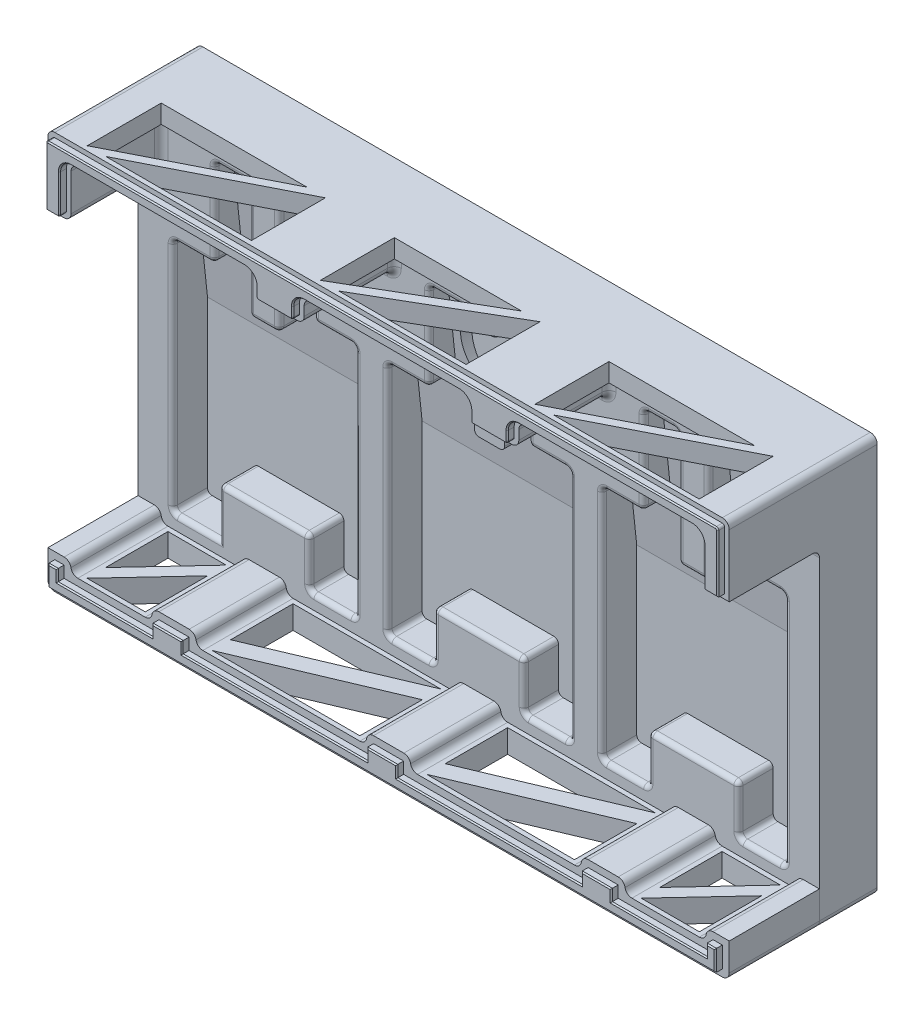
SolidWorks part; units mm, degrees
material "PP generico"
ref_plane "Piano frontale" through (0, 0, 0) normal (0, 0, 1) x (1, 0, 0)
ref_plane "Piano superiore" through (0, 0, 0) normal (0, 1, 0) x (1, 0, 0)
ref_plane "Piano destro" through (0, 0, 0) normal (1, 0, 0) x (0, 0, -1)
sketch "Schizzo1" plane through (0, 0, 0) normal (0, 0, 1) x (1, 0, 0)
  line L1 (-147.3, 86) -> (147.3, 86)
  line L2 (-147.3, 86) -> (-147.3, -86)
  line L3 (-147.3, -86) -> (147.3, -86)
  line L4 (147.3, 86) -> (147.3, -86)
  dimension "D1" = 294.6
  dimension "D2" = 172
  dimension "D3" = 147.3
  dimension "D4" = 86
extrude "Estrusione-Estrusione1" add sketch "Schizzo1" along normal blind 10 contours L1 L4 L3 L2
sketch "Schizzo2" plane through (0, 0, 10) normal (0, 0, 1) x (1, 0, 0)
  line L0 (-73.3, -70) -> (-53.3, -70)
  line L1 (-147.3, 86) -> (147.3, 86)
  line L2 (-147.3, 86) -> (-147.3, -86)
  line L3 (-6.3232, -86) -> (147.3, -86)
  line L4 (147.3, 86) -> (147.3, -86)
  line L9 (-114.3, 70) -> (-99.3, 70)
  line L10 (-132.3, 32) -> (-132.3, -70)
  line L11 (-132.3, -70) -> (-112.3, -70)
  line L12 (-53.3, 32) -> (-53.3, -70)
  line L14 (-39.5, 32) -> (-39.5, -69.8088)
  line L15 (-39.5, -69.8088) -> (-19.5, -69.8088)
  line L16 (39.5, 32) -> (39.5, -69.8088)
  line L18 (53.3, 32) -> (53.3, -69.8088)
  line L19 (53.3, -69.8088) -> (73.3, -69.8088)
  line L20 (132.3, 32) -> (132.3, -69.8088)
  line L21 (-112.3, -49) -> (-73.3, -49)
  line L22 (-112.3, -49) -> (-112.3, -70)
  line L24 (-73.3, -49) -> (-73.3, -70)
  line L25 (19.5, -69.8088) -> (39.5, -69.8088)
  line L26 (-19.5, -48.8088) -> (19.5, -48.8088)
  line L27 (-19.5, -48.8088) -> (-19.5, -69.8088)
  line L29 (19.5, -48.8088) -> (19.5, -69.8088)
  line L30 (73.3, -48.8088) -> (112.3, -48.8088)
  line L31 (73.3, -48.8088) -> (73.3, -69.8088)
  line L33 (112.3, -48.8088) -> (112.3, -69.8088)
  line L34 (112.3, -69.8088) -> (132.3, -69.8088)
  line L35 (-86.3, 70) -> (-71.3, 70)
  line L38 (-132.3, 32) -> (-114.3, 32)
  line L39 (-114.3, 70) -> (-114.3, 32)
  line L42 (-53.3, 32) -> (-71.3, 32)
  line L43 (-71.3, 70) -> (-71.3, 32)
  line L45 (-99.3, 70) -> (-99.3, 20)
  line L46 (-99.3, 20) -> (-86.3, 20)
  line L47 (-86.3, 70) -> (-86.3, 20)
  line L48 (-21.5, 70) -> (-21.5, 32)
  line L49 (-39.5, 32) -> (-21.5, 32)
  line L50 (-21.5, 70) -> (-6.5, 70)
  line L51 (-6.5, 70) -> (-6.5, 20)
  line L52 (6.5, 70) -> (6.5, 20)
  line L53 (6.5, 70) -> (21.5, 70)
  line L54 (21.5, 70) -> (21.5, 32)
  line L55 (39.5, 32) -> (21.5, 32)
  line L56 (-6.5, 20) -> (6.5, 20)
  line L57 (71.3, 70) -> (71.3, 32)
  line L58 (53.3, 32) -> (71.3, 32)
  line L59 (71.3, 70) -> (86.3, 70)
  line L60 (86.3, 70) -> (86.3, 20)
  line L61 (99.3, 70) -> (99.3, 20)
  line L62 (99.3, 70) -> (114.3, 70)
  line L63 (114.3, 70) -> (114.3, 32)
  line L64 (132.3, 32) -> (114.3, 32)
  line L65 (86.3, 20) -> (99.3, 20)
  dimension "D3" = 15
  dimension "D4" = 13.8
  dimension "D5" = 140
  dimension "D6" = 38
  dimension "D7" = 38
  dimension "D8" = 20
  dimension "D9" = 20
  dimension "D10" = 21
  dimension "D11" = 20
  dimension "D12" = 20
  dimension "D13" = 16
  dimension "D14" = 0
  dimension "D16" = 20
  dimension "D17" = 20
  dimension "D18" = 21
  dimension "D19" = 21
  dimension "D20" = 18
  dimension "D21" = 18
  dimension "D22" = 15
  dimension "D23" = 15
  dimension "D24" = 50
  dimension "D25" = 3
extrude "Estrusione-Estrusione2" add sketch "Schizzo2" along normal blind 15
sketch "Schizzo4" plane through (132.3, 0, 0) normal (-1, 0, 0) x (0, 0, 1)
  line L0 (10, 70) -> (10, 3.34)
  line L1 (10, 32) -> (10, -69.8088) construction
  line L2 (10, 3.34) -> (17.12, 70)
  line L4 (17.12, 70) -> (10, 70)
  dimension "D3" = 73.1488
extrude "Estrusione-Estrusione3" add sketch "Schizzo4" along normal up to surface (264.6 mm away) up to face at (-132.3, -19, 17.5)
sketch "Schizzo5" plane through (0, 0, 25) normal (0, 0, 1) x (1, 0, 0)
  line L0 (-147.3, 86) -> (-147.3, 56)
  line L1 (-147.3, 86) -> (-147.3, -86) construction
  line L2 (-147.3, 56) -> (-137.3, 56)
  line L3 (-137.3, 56) -> (-137.3, 78)
  line L4 (-137.3, 78) -> (-56.3, 78)
  line L5 (-56.3, 78) -> (-56.3, 68)
  line L6 (-56.3, 68) -> (-36.5, 68)
  line L7 (-36.5, 68) -> (-36.5, 78)
  line L8 (-36.5, 78) -> (36.5, 78)
  line L9 (36.5, 78) -> (36.5, 68)
  line L10 (36.5, 68) -> (56.3, 68)
  line L11 (56.3, 68) -> (56.3, 78)
  line L12 (56.3, 78) -> (137.3, 78)
  line L13 (137.3, 78) -> (137.3, 56)
  line L14 (137.3, 56) -> (147.3, 56)
  line L15 (147.3, -86) -> (147.3, 86) construction
  line L16 (147.3, 56) -> (147.3, 86)
  line L17 (147.3, 86) -> (-147.3, 86)
  line L18 (-21.5, 70) -> (-21.5, 32) construction
  line L19 (-71.3, 32) -> (-71.3, 70) construction
  line L20 (21.5, 32) -> (21.5, 70) construction
  line L22 (71.3, 70) -> (71.3, 32) construction
  dimension "D1" = 30
  dimension "D2" = 30
  dimension "D3" = 10
  dimension "D4" = 10
  dimension "D5" = 15
  dimension "D6" = 15
  dimension "D7" = 8
  dimension "D8" = 15
  dimension "D9" = 8
  dimension "D10" = 15
  dimension "D11" = 8
extrude "Estrusione-Estrusione4" add sketch "Schizzo5" along normal blind 39
fillet "Raccordo1" radius 3 27 edges at (137.3, 67, 25) (36.5, 73, 25) (56.3, 73, 25) (-36.5, 73, 25) (-56.3, 73, 25) (147.3, 86, 32) (137.3, 78, 44.5) (137.3, 56, 44.5) (142.3, 56, 25) (96.8, 78, 25) (56.3, 78, 44.5) (36.5, 78, 44.5) (36.5, 68, 44.5) (56.3, 68, 44.5) (46.4, 68, 25) (0, 78, 25) (-36.5, 68, 44.5) (-36.5, 78, 44.5) (-46.4, 68, 25) (-56.3, 68, 44.5) (-147.3, 86, 32) (-137.3, 56, 44.5) (-137.3, 78, 44.5) (-96.8, 78, 25) (-142.3, 56, 25) (-137.3, 67, 25) (-56.3, 78, 44.5)
fillet "Raccordo2" radius 2 31 edges at (-114.3, 51, 25) (-123.3, 32, 25) (-53.3, -70, 17.5) (-132.3, -70, 17.5) (-112.3, -49, 17.5) (-73.3, -70, 17.5) (-73.3, -49, 17.5) (-53.3, 32, 19.0306) (-99.3, 70, 21.06) (-86.3, 70, 21.06) (-71.3, 70, 21.06) (-71.3, 32, 19.0306) (-86.3, 20, 18.3897) (-99.3, 20, 18.3897) (-71.3, 51, 25) (-86.3, 45, 25) (-99.3, 45, 25) (-92.8, 20, 25) (-106.8, 70, 25) (-78.8, 70, 25) (-62.3, 32, 25) (-53.3, -19, 25) (-63.3, -70, 25) (-73.3, -59.5, 25) (-92.8, -49, 25) (-112.3, -59.5, 25) (-122.3, -70, 25) (-132.3, -19, 25) (-114.3, 70, 21.06) (-132.3, 32, 19.0306) (-114.3, 32, 19.0306)
fillet "Raccordo4" radius 2 64 edges at (114.3, 51, 25) (106.8, 70, 25) (78.8, 70, 25) (53.3, -18.9044, 25) (132.3, -69.8088, 17.5) (132.3, 32, 19.0306) (86.3, 20, 18.3897) (114.3, 32, 19.0306) (114.3, 70, 21.06) (99.3, 70, 21.06) (86.3, 70, 21.06) (71.3, 51, 25) (71.3, 70, 21.06) (53.3, 32, 19.0306) (73.3, -69.8088, 17.5) (73.3, -48.8088, 17.5) (112.3, -69.8088, 17.5) (132.3, -18.9044, 25) (123.3, 32, 25) (99.3, 45, 25) (86.3, 45, 25) (92.8, 20, 25) (62.3, 32, 25) (92.8, -48.8088, 25) (63.3, -69.8088, 25) (73.3, -59.3088, 25) (112.3, -59.3088, 25) (122.3, -69.8088, 25) (112.3, -48.8088, 17.5) (99.3, 20, 18.3897) (71.3, 32, 19.0306) (53.3, -69.8088, 17.5) (-39.5, -69.8088, 17.5) (19.5, -69.8088, 17.5) (39.5, -69.8088, 17.5) (19.5, -48.8088, 17.5) (-19.5, -48.8088, 17.5) (-19.5, -69.8088, 17.5) (-39.5, 32, 19.0306) (-21.5, 70, 21.06) (6.5, 70, 21.06) (21.5, 70, 21.06) (39.5, 32, 19.0306) (-21.5, 32, 19.0306) (-6.5, 20, 18.3897) (6.5, 20, 18.3897) (21.5, 32, 19.0306) (30.5, 32, 25) (21.5, 51, 25) (6.5, 45, 25) (-21.5, 51, 25) (-30.5, 32, 25) (-6.5, 45, 25) (0, 20, 25) (39.5, -18.9044, 25) (29.5, -69.8088, 25) (19.5, -59.3088, 25) (0, -48.8088, 25) (-19.5, -59.3088, 25) (-39.5, -18.9044, 25) (-29.5, -69.8088, 25) (-14, 70, 25) (14, 70, 25) (-6.5, 70, 21.06)
sketch "Schizzo8" plane through (0, 0, 25) normal (0, 0, 1) x (1, 0, 0)
  line L0 (-147.3, -86) -> (-147.3, -71)
  line L1 (-147.3, 53) -> (-147.3, -86) construction
  line L2 (-147.3, -71) -> (-137.3, -71)
  line L3 (-137.3, -71) -> (-137.3, -76)
  line L4 (-137.3, -76) -> (-102.3, -76)
  line L5 (-102.3, -76) -> (-102.3, -71)
  line L6 (-102.3, -71) -> (-83.3, -71)
  line L7 (-83.3, -71) -> (-83.3, -76)
  line L8 (-83.3, -76) -> (-9.5, -76)
  line L9 (-9.5, -76) -> (-9.5, -71)
  line L10 (-9.5, -71) -> (9.5, -71)
  line L11 (9.5, -71) -> (9.5, -76)
  line L12 (9.5, -76) -> (83.3, -76)
  line L13 (83.3, -76) -> (83.3, -71)
  line L14 (83.3, -71) -> (102.3, -71)
  line L15 (102.3, -71) -> (102.3, -76)
  line L16 (102.3, -76) -> (137.3, -76)
  line L17 (137.3, -76) -> (137.3, -71)
  line L18 (137.3, -71) -> (147.3, -71)
  line L19 (147.3, -86) -> (147.3, 53) construction
  line L20 (147.3, -71) -> (147.3, -86)
  line L21 (147.3, -86) -> (-147.3, -86)
  line L22 (-110.3, -51) -> (-110.3, -72) construction
  line L23 (-75.3, -68) -> (-75.3, -51) construction
  line L26 (75.3, -50.8088) -> (75.3, -67.8088) construction
  line L27 (110.3, -67.8088) -> (110.3, -50.8088) construction
  line L28 (-17.5, -50.8088) -> (-17.5, -67.8088) construction
  line L29 (17.5, -67.8088) -> (17.5, -50.8088) construction
  dimension "D1" = 10
  dimension "D2" = 10
  dimension "D3" = 15
  dimension "D4" = 15
  dimension "D5" = 15
  dimension "D6" = 15
  dimension "D7" = 15
  dimension "D8" = 8
  dimension "D9" = 8
  dimension "D10" = 8
  dimension "D11" = 8
  dimension "D12" = 8
  dimension "D13" = 8
  dimension "D14" = 10
  dimension "D15" = 10
  dimension "D16" = 10
  dimension "D17" = 10
extrude "Estrusione-Estrusione5" add sketch "Schizzo8" along normal up to surface (39 mm away) up to face at (0, 71.8414, 64)
fillet "Raccordo8" radius 3 2 edges at (147.3, -86, 12.5) (-147.3, -86, 12.5)
sketch "Schizzo10" plane through (0, 0, 64) normal (0, 0, 1) x (1, 0, 0)
  line L16 (-38.5, 71) -> (-38.5, 75)
  line L17 (-38.5, 71) -> (-38.5, 75)
  line L18 (140.3, -74) -> (140.3, -79)
  line L19 (140.3, -74) -> (140.3, -79)
  line L20 (99.3, -79) -> (99.3, -74)
  line L21 (99.3, -79) -> (99.3, -74)
  line L22 (86.3, -74) -> (86.3, -79)
  line L23 (86.3, -74) -> (86.3, -79)
  line L24 (6.5, -79) -> (6.5, -74)
  line L25 (6.5, -79) -> (6.5, -74)
  line L26 (-6.5, -74) -> (-6.5, -79)
  line L27 (-6.5, -74) -> (-6.5, -79)
  line L28 (-86.3, -79) -> (-86.3, -74)
  line L29 (-86.3, -79) -> (-86.3, -74)
  line L30 (38.5, 75) -> (38.5, 71)
  line L31 (38.5, 75) -> (38.5, 71)
  line L32 (-99.3, -74) -> (-99.3, -79)
  line L33 (-99.3, -74) -> (-99.3, -79)
  line L34 (-140.3, -79) -> (-140.3, -74)
  line L35 (-140.3, -79) -> (-140.3, -74)
  line L72 (-144.3, -83) -> (144.3, -83)
  line L73 (144.3, -83) -> (144.3, -74)
  line L74 (144.3, -74) -> (140.3, -74)
  line L75 (140.3, -79) -> (99.3, -79)
  line L76 (99.3, -74) -> (86.3, -74)
  line L77 (86.3, -79) -> (6.5, -79)
  line L78 (6.5, -74) -> (-6.5, -74)
  line L79 (-6.5, -79) -> (-86.3, -79)
  line L80 (-86.3, -74) -> (-99.3, -74)
  line L81 (-99.3, -79) -> (-140.3, -79)
  line L82 (-140.3, -74) -> (-144.3, -74)
  line L83 (-144.3, -74) -> (-144.3, -83)
  line L84 (-144.3, -83) -> (144.3, -83)
  line L85 (144.3, -83) -> (144.3, -74)
  line L86 (144.3, -74) -> (140.3, -74)
  line L87 (140.3, -79) -> (99.3, -79)
  line L88 (99.3, -74) -> (86.3, -74)
  line L89 (86.3, -79) -> (6.5, -79)
  line L90 (6.5, -74) -> (-6.5, -74)
  line L91 (-6.5, -79) -> (-86.3, -79)
  line L92 (-86.3, -74) -> (-99.3, -74)
  line L93 (-99.3, -79) -> (-140.3, -79)
  line L94 (-140.3, -74) -> (-144.3, -74)
  line L95 (-144.3, -74) -> (-144.3, -83)
  line L100 (140.3, 58) -> (145.3, 58)
  line L101 (145.3, 58) -> (145.3, 83)
  line L102 (144.3, 84) -> (-144.3, 84)
  line L103 (-145.3, 83) -> (-145.3, 58)
  line L104 (-145.3, 58) -> (-140.3, 58)
  line L105 (-139.3, 59) -> (-139.3, 75)
  line L106 (-134.3, 80) -> (-59.3, 80)
  line L107 (-54.3, 75) -> (-54.3, 71)
  line L108 (-53.3, 70) -> (-39.5, 70)
  line L110 (-33.5, 80) -> (33.5, 80)
  line L112 (39.5, 70) -> (53.3, 70)
  line L113 (54.3, 71) -> (54.3, 75)
  line L114 (59.3, 80) -> (134.3, 80)
  line L115 (139.3, 75) -> (139.3, 59)
  line L116 (140.3, 58) -> (145.3, 58)
  line L117 (145.3, 58) -> (145.3, 83)
  line L118 (144.3, 84) -> (-144.3, 84)
  line L119 (-145.3, 83) -> (-145.3, 58)
  line L120 (-145.3, 58) -> (-140.3, 58)
  line L121 (-139.3, 59) -> (-139.3, 75)
  line L122 (-134.3, 80) -> (-59.3, 80)
  line L123 (-54.3, 75) -> (-54.3, 71)
  line L124 (-53.3, 70) -> (-39.5, 70)
  line L126 (-33.5, 80) -> (33.5, 80)
  line L128 (39.5, 70) -> (53.3, 70)
  line L129 (54.3, 71) -> (54.3, 75)
  line L130 (59.3, 80) -> (134.3, 80)
  line L131 (139.3, 75) -> (139.3, 59)
  arc A85 (145.3, 83) -> (144.3, 84) centre (144.3, 83) ccw
  arc A86 (-144.3, 84) -> (-145.3, 83) centre (-144.3, 83) ccw
  arc A104 (-140.3, 58) -> (-139.3, 59) centre (-140.3, 59) ccw
  arc A105 (-134.3, 80) -> (-139.3, 75) centre (-134.3, 75) ccw
  arc A106 (-54.3, 75) -> (-59.3, 80) centre (-59.3, 75) ccw
  arc A107 (-54.3, 71) -> (-53.3, 70) centre (-53.3, 71) ccw
  arc A108 (-39.5, 70) -> (-38.5, 71) centre (-39.5, 71) ccw
  arc A109 (-33.5, 80) -> (-38.5, 75) centre (-33.5, 75) ccw
  arc A110 (38.5, 75) -> (33.5, 80) centre (33.5, 75) ccw
  arc A111 (38.5, 71) -> (39.5, 70) centre (39.5, 71) ccw
  arc A112 (53.3, 70) -> (54.3, 71) centre (53.3, 71) ccw
  arc A113 (59.3, 80) -> (54.3, 75) centre (59.3, 75) ccw
  arc A114 (139.3, 75) -> (134.3, 80) centre (134.3, 75) ccw
  arc A115 (139.3, 59) -> (140.3, 58) centre (140.3, 59) ccw
  arc A117 (145.3, 83) -> (144.3, 84) centre (144.3, 83) ccw
  arc A118 (-144.3, 84) -> (-145.3, 83) centre (-144.3, 83) ccw
  arc A120 (-140.3, 58) -> (-139.3, 59) centre (-140.3, 59) ccw
  arc A121 (-134.3, 80) -> (-139.3, 75) centre (-134.3, 75) ccw
  arc A122 (-54.3, 75) -> (-59.3, 80) centre (-59.3, 75) ccw
  arc A123 (-54.3, 71) -> (-53.3, 70) centre (-53.3, 71) ccw
  arc A124 (-39.5, 70) -> (-38.5, 71) centre (-39.5, 71) ccw
  arc A125 (-33.5, 80) -> (-38.5, 75) centre (-33.5, 75) ccw
  arc A126 (38.5, 75) -> (33.5, 80) centre (33.5, 75) ccw
  arc A127 (38.5, 71) -> (39.5, 70) centre (39.5, 71) ccw
  arc A128 (53.3, 70) -> (54.3, 71) centre (53.3, 71) ccw
  arc A129 (59.3, 80) -> (54.3, 75) centre (59.3, 75) ccw
  arc A130 (139.3, 75) -> (134.3, 80) centre (134.3, 75) ccw
  arc A131 (139.3, 59) -> (140.3, 58) centre (140.3, 59) ccw
  dimension "D1" = 2
  dimension "D2" = 3
extrude "Estrusione-Estrusione6" add sketch "Schizzo10" along normal blind 3
sketch "Schizzo11" plane through (0, 0, 0) normal (0, 0, 1) x (1, 0, 0)
  line L84 (-144.3, -83) -> (144.3, -83)
  line L85 (144.3, -83) -> (144.3, -74)
  line L86 (144.3, -74) -> (140.3, -74)
  line L87 (134.3839, -79) -> (107.2161, -79)
  line L88 (101.3, -74) -> (84.3, -74)
  line L89 (78.3839, -79) -> (14.4161, -79)
  line L90 (8.5, -74) -> (-8.5, -74)
  line L91 (-14.4161, -79) -> (-78.3839, -79)
  line L92 (-84.3, -74) -> (-101.3, -74)
  line L93 (-107.2161, -79) -> (-134.3839, -79)
  line L94 (-140.3, -74) -> (-144.3, -74)
  line L95 (-144.3, -74) -> (-144.3, -83)
  line L116 (140.3, 58) -> (144.3, 58)
  line L117 (145.3, 59) -> (145.3, 83)
  line L118 (144.3, 84) -> (-144.3, 84)
  line L119 (-145.3, 83) -> (-145.3, 59)
  line L120 (-144.3, 58) -> (-140.3, 58)
  line L121 (-139.3, 59) -> (-139.3, 75)
  line L122 (-134.3, 80) -> (-59.3, 80)
  line L123 (-54.3, 75) -> (-54.3, 71)
  line L124 (-53.3, 70) -> (-39.5, 70)
  line L125 (-38.5, 71) -> (-38.5, 75)
  line L126 (-33.5, 80) -> (33.5, 80)
  line L127 (38.5, 75) -> (38.5, 71)
  line L128 (39.5, 70) -> (53.3, 70)
  line L129 (54.3, 71) -> (54.3, 75)
  line L130 (59.3, 80) -> (134.3, 80)
  line L131 (139.3, 75) -> (139.3, 59)
  arc A96 (134.3839, -79) -> (140.3, -74) centre (134.3839, -73) ccw
  arc A97 (101.3, -74) -> (107.2161, -79) centre (107.2161, -73) ccw
  arc A98 (78.3839, -79) -> (84.3, -74) centre (78.3839, -73) ccw
  arc A99 (8.5, -74) -> (14.4161, -79) centre (14.4161, -73) ccw
  arc A100 (-14.4161, -79) -> (-8.5, -74) centre (-14.4161, -73) ccw
  arc A101 (-84.3, -74) -> (-78.3839, -79) centre (-78.3839, -73) ccw
  arc A102 (-107.2161, -79) -> (-101.3, -74) centre (-107.2161, -73) ccw
  arc A103 (-140.3, -74) -> (-134.3839, -79) centre (-134.3839, -73) ccw
  arc A116 (144.3, 58) -> (145.3, 59) centre (144.3, 59) ccw
  arc A117 (145.3, 83) -> (144.3, 84) centre (144.3, 83) ccw
  arc A118 (-144.3, 84) -> (-145.3, 83) centre (-144.3, 83) ccw
  arc A119 (-145.3, 59) -> (-144.3, 58) centre (-144.3, 59) ccw
  arc A120 (-140.3, 58) -> (-139.3, 59) centre (-140.3, 59) ccw
  arc A121 (-134.3, 80) -> (-139.3, 75) centre (-134.3, 75) ccw
  arc A122 (-54.3, 75) -> (-59.3, 80) centre (-59.3, 75) ccw
  arc A123 (-54.3, 71) -> (-53.3, 70) centre (-53.3, 71) ccw
  arc A124 (-39.5, 70) -> (-38.5, 71) centre (-39.5, 71) ccw
  arc A125 (-33.5, 80) -> (-38.5, 75) centre (-33.5, 75) ccw
  arc A126 (38.5, 75) -> (33.5, 80) centre (33.5, 75) ccw
  arc A127 (38.5, 71) -> (39.5, 70) centre (39.5, 71) ccw
  arc A128 (53.3, 70) -> (54.3, 71) centre (53.3, 71) ccw
  arc A129 (59.3, 80) -> (54.3, 75) centre (59.3, 75) ccw
  arc A130 (139.3, 75) -> (134.3, 80) centre (134.3, 75) ccw
  arc A131 (139.3, 59) -> (140.3, 58) centre (140.3, 59) ccw
extrude "Taglio-Estrusione1" cut sketch "Schizzo11" along normal blind 4
fillet "Raccordo9" radius 3 4 edges at (9.5, -76, 44.5) (-83.3, -76, 44.5) (-102.3, -71, 44.5) (-9.5, -71, 44.5)
fillet "Raccordo10" radius 3 4 edges at (-9.5, -76, 44.5) (-137.3, -71, 44.5) (-83.3, -71, 44.5) (-102.3, -76, 44.5)
fillet "Raccordo11" radius 3 2 edges at (-137.3, -76, 44.5) (137.3, -71, 44.5)
fillet "Raccordo12" radius 3 2 edges at (137.3, -76, 44.5) (102.3, -71, 44.5)
fillet "Raccordo13" radius 3 3 edges at (102.3, -76, 44.5) (9.5, -71, 44.5) (83.3, -71, 44.5)
fillet "Raccordo14" radius 3 2 edges at (-147.3, -86, 44.5) (147.3, -86, 44.5)
chamfer "Smusso1" distance 0.5 angle 45 20 edges at (144.3, -78.5, 67) (0, -83, 67) (-144.3, -78.5, 67) (-142.3, -74, 67) (-140.3, -76.5, 67) (-119.8, -79, 67) (-99.3, -76.5, 67) (-92.8, -74, 67) (-86.3, -76.5, 67) (-46.4, -79, 67) (-6.5, -76.5, 67) (0, -74, 67) (6.5, -76.5, 67) (46.4, -79, 67) (86.3, -76.5, 67) (92.8, -74, 67) (99.3, -76.5, 67) (119.8, -79, 67) (140.3, -76.5, 67) (142.3, -74, 67)
chamfer "Smusso2" distance 0.5 angle 45 30 edges at (142.8, 58, 67) (139.5929, 58.2929, 67) (139.3, 67, 67) (137.8355, 78.5355, 67) (96.8, 80, 67) (55.7645, 78.5355, 67) (54.3, 73, 67) (54.0071, 70.2929, 67) (46.4, 70, 67) (38.7929, 70.2929, 67) (38.5, 73, 67) (37.0355, 78.5355, 67) (0, 80, 67) (-37.0355, 78.5355, 67) (-38.5, 73, 67) (-38.7929, 70.2929, 67) (-46.4, 70, 67) (-54.0071, 70.2929, 67) (-54.3, 73, 67) (-55.7645, 78.5355, 67) (-96.8, 80, 67) (-137.8355, 78.5355, 67) (-139.3, 67, 67) (-139.5929, 58.2929, 67) (-142.8, 58, 67) (-145.3, 70.5, 67) (-145.0071, 83.7071, 67) (0, 84, 67) (145.0071, 83.7071, 67) (145.3, 70.5, 67)
sketch "Schizzo12" plane through (0, 78, 0) normal (0, -1, 0) x (1, 0, 0)
  line L0 (-132.3, 30) -> (-132.3, 62)
  line L1 (-132.3, 62) -> (-69.3, 30)
  line L2 (-69.3, 30) -> (-132.3, 30)
  line L3 (-134.3, 64) -> (-134.3, 28) construction
  line L4 (-134.3, 28) -> (-59.3, 28) construction
  line L5 (-124.3, 62) -> (-61.3, 62)
  line L6 (-61.3, 62) -> (-61.3, 30)
  line L7 (-61.3, 30) -> (-124.3, 62)
  line L8 (-134.3, 64) -> (-59.3, 64) construction
  line L9 (-59.3, 28) -> (-59.3, 64) construction
  line L10 (132.3, 62) -> (132.3, 30)
  line L11 (132.3, 30) -> (69.3, 62)
  line L12 (61.3, 62) -> (124.3, 30)
  line L13 (124.3, 30) -> (61.3, 30)
  line L14 (61.3, 30) -> (61.3, 62)
  line L15 (69.3, 62) -> (132.3, 62)
  line L16 (59.3, 64) -> (59.3, 28) construction
  line L17 (-33.5, 28) -> (33.5, 28) construction
  line L18 (-31.5, 30) -> (23.5, 30)
  line L19 (23.5, 30) -> (-31.5, 62)
  line L20 (-31.5, 62) -> (-31.5, 30)
  line L21 (-23.5, 62) -> (31.5, 62)
  line L22 (31.5, 62) -> (31.5, 30)
  line L23 (31.5, 30) -> (-23.5, 62)
  line L24 (-33.5, 64) -> (-33.5, 28) construction
  line L25 (33.5, 28) -> (33.5, 64) construction
  line L27 (-33.5, 64) -> (33.5, 64) construction
  dimension "D1" = 2
  dimension "D2" = 2
  dimension "D3" = 2
  dimension "D4" = 2
  dimension "D5" = 2
  dimension "D6" = 2
  dimension "D7" = 10
  dimension "D8" = 10
  dimension "D10" = 2
  dimension "D11" = 2
  dimension "D12" = 2
  dimension "D13" = 10
  dimension "D14" = 10
  dimension "D15" = 2
  dimension "D16" = 2
  dimension "D9" = 2
extrude "Taglio-Estrusione2" cut sketch "Schizzo12" against normal blind 10
sketch "Schizzo14" plane through (0, -76, 0) normal (0, 1, 0) x (1, 0, 0)
  line L0 (-78.3, -27) -> (-14.4161, -27)
  line L1 (-14.4161, -27) -> (-78.3, -54)
  line L2 (-78.3, -54) -> (-78.3, -27)
  line L3 (-78.3, -62) -> (-14.4161, -35)
  line L4 (-14.4161, -35) -> (-14.4161, -62)
  line L5 (-14.4161, -62) -> (-78.3, -62)
  line L7 (-6.5, -64) -> (-86.3, -64) construction
  line L8 (-12.4161, -25) -> (-80.3, -25) construction
  line L9 (-12.4161, -64) -> (-12.4161, -25) construction
  line L10 (-144.3, -25) -> (144.3, -25) construction
  line L11 (-80.3, -25) -> (-80.3, -64) construction
  line L12 (78.3839, -62) -> (14.5, -62)
  line L13 (78.3839, -35) -> (78.3839, -62)
  line L14 (14.5, -62) -> (78.3839, -35)
  line L15 (78.3839, -27) -> (14.5, -54)
  line L16 (14.5, -54) -> (14.5, -27)
  line L17 (14.5, -27) -> (78.3839, -27)
  line L20 (12.5, -25) -> (12.5, -64) construction
  line L21 (107.2161, -27) -> (132.3839, -27)
  line L22 (132.3839, -27) -> (107.2161, -54)
  line L23 (107.2161, -54) -> (107.2161, -27)
  line L24 (132.3839, -35) -> (132.3839, -62)
  line L25 (132.3839, -62) -> (107.2161, -62)
  line L26 (107.2161, -62) -> (132.3839, -35)
  line L27 (105.2161, -25) -> (105.2161, -64) construction
  line L28 (134.3839, -64) -> (134.3839, -25) construction
  line L29 (134.3839, -64) -> (105.2161, -64) construction
  line L30 (134.3839, -25) -> (105.2161, -25) construction
  line L31 (-132.3839, -27) -> (-107.2161, -27)
  line L32 (-132.3839, -54) -> (-132.3839, -27)
  line L33 (-107.2161, -27) -> (-132.3839, -54)
  line L34 (-132.3839, -62) -> (-107.2161, -35)
  line L35 (-107.2161, -62) -> (-132.3839, -62)
  line L36 (-107.2161, -35) -> (-107.2161, -62)
  line L37 (-134.3839, -25) -> (-134.3839, -64) construction
  dimension "D1" = 2
  dimension "D2" = 2
  dimension "D3" = 2
  dimension "D4" = 10
  dimension "D5" = 2
  dimension "D6" = 2
  dimension "D7" = 2
  dimension "D9" = 2
  dimension "D10" = 2
  dimension "D11" = 2
  dimension "D12" = 2
  dimension "D13" = 10
  dimension "D14" = 10
  dimension "D15" = 2
  dimension "D17" = 2
  dimension "D8" = 2
  dimension "D16" = 2
extrude "Taglio-Estrusione3" cut sketch "Schizzo14" against normal blind 10
fillet "Raccordo15" radius 3 1 edges at (83.3, -76, 44.5)
sketch "Schizzo15" plane through (0, 20, 0) normal (0, -1, 0) x (1, 0, 0)
  line L1 (-8.824, 26.8346) -> (9.6819, 26.8346)
  line L2 (-8.824, 26.8346) -> (-8.824, 20.3575)
  line L3 (-8.824, 20.3575) -> (9.6819, 20.3575)
  line L4 (9.6819, 26.8346) -> (9.6819, 20.3575)
extrude "Taglio-Estrusione4" cut sketch "Schizzo15" against normal blind 37
sketch "Schizzo16" plane through (0, 0, 20.3575) normal (0, 0, 1) x (1, 0, 0)
  line L1 (-4.5, 20) -> (4.5, 20) construction
  line L2 (-6.5, 22) -> (-6.5, 57) construction
  circle A0 centre (-0.5, 48.5) radius 17.5
  dimension "D1" = 35
  dimension "D2" = 28.5
  dimension "D3" = 6
extrude "Taglio-Estrusione5" cut sketch "Schizzo16" against normal up to surface (10.3575 mm away) and the other way blind 37 up to face at (0, -53.1324, 10)
